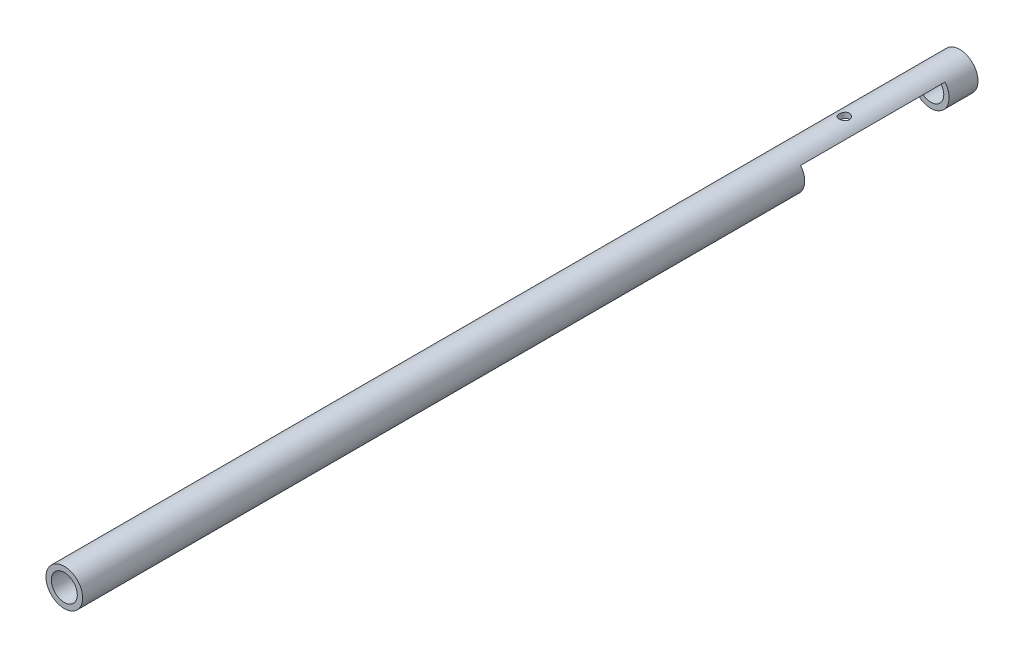
SolidWorks part; units mm, degrees
ref_plane "Front Plane" through (0, 0, 0) normal (0, 0, 1) x (1, 0, 0)
ref_plane "Top Plane" through (0, 0, 0) normal (0, 1, 0) x (1, 0, 0)
ref_plane "Right Plane" through (0, 0, 0) normal (1, 0, 0) x (0, 0, -1)
sketch "Sketch1" plane through (0, 0, 0) normal (0, 0, 1) x (1, 0, 0)
  circle A0 centre (0, 0) radius 2.25
  circle A1 centre (0, 0) radius 3.175
  dimension "D1" = 4.5
  dimension "D2" = 6.35
extrude "Boss-Extrude1" add sketch "Sketch1" along normal blind 35
sketch "Sketch2" plane through (0, 0, 0) normal (0, 1, 0) x (1, 0, 0)
  line L1 (-5.5281, -30) -> (7.5019, -30)
  line L2 (-5.5281, -30) -> (-5.5281, -5)
  line L3 (-5.5281, -5) -> (7.5019, -5)
  line L4 (7.5019, -30) -> (7.5019, -5)
  dimension "D1" = 5
  dimension "D2" = 25
extrude "Cut-Extrude1" cut sketch "Sketch2" against normal blind 5 and the other way blind 2
sketch "Sketch3" plane through (0, 2, 0) normal (0, -1, 0) x (-1, 0, 0)
  line L0 (2.25, -30) -> (-2.25, -30) construction
  circle A0 centre (0, -20) radius 0.889
  point P2 (0, -30)
  dimension "D1" = 1.778
  dimension "D2" = 10
extrude "2-56 hole" cut sketch "Sketch3" against normal blind 3
sketch "Sketch4" plane through (0, 0, 35) normal (0, 0, 1) x (1, 0, 0)
  circle A0 centre (0, 0) radius 3.175 construction
  circle A1 centre (0, 0) radius 2.25 construction
  circle A2 centre (0, 0) radius 3.175
  circle A3 centre (0, 0) radius 2.25
extrude "Boss-Extrude2" add sketch "Sketch4" along normal blind 120
